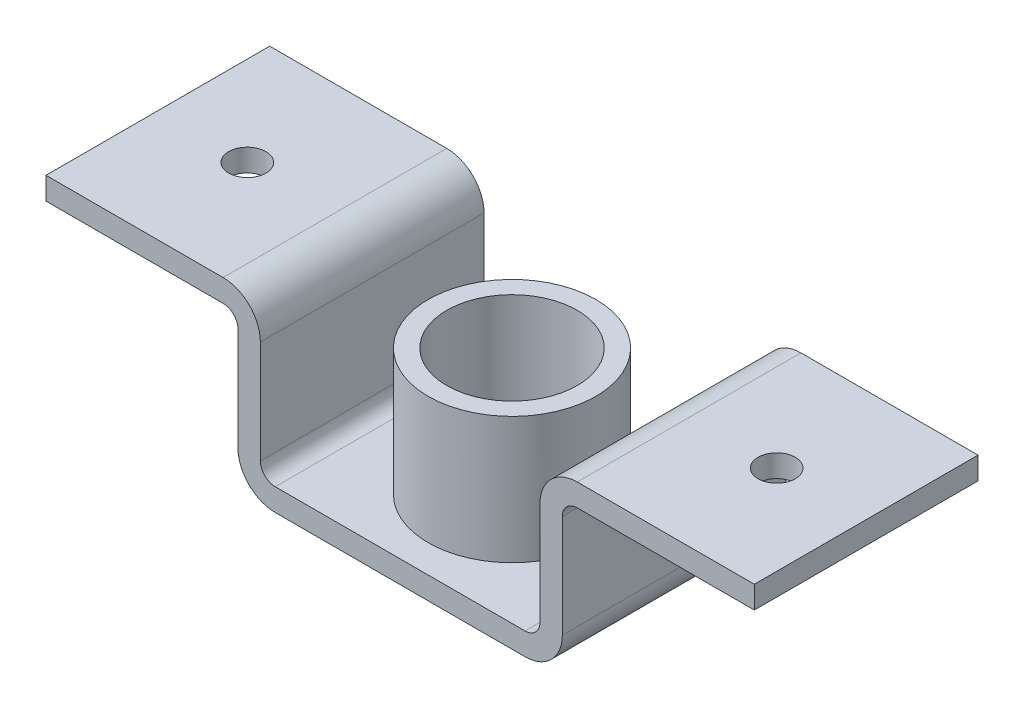
SolidWorks part; units mm, degrees
ref_plane "Front Plane" through (0, 0, 0) normal (0, 0, 1) x (1, 0, 0)
ref_plane "Top Plane" through (0, 0, 0) normal (0, 1, 0) x (1, 0, 0)
ref_plane "Right Plane" through (0, 0, 0) normal (1, 0, 0) x (0, 0, -1)
sketch "Sketch1" plane through (0, 0, 0) normal (0, 0, 1) x (1, 0, 0)
  line L0 (0, 437.3723) -> (0, -104.5891) construction
  line L1 (167.5, 0) -> (-167.5, 0)
  line L2 (-217.5, 50) -> (-217.5, 188)
  line L3 (-237.5, 208) -> (-475, 208)
  line L4 (-475, 208) -> (-475, 238)
  line L5 (-475, 238) -> (-237.5, 238)
  line L6 (-187.5, 188) -> (-187.5, 50)
  line L7 (-167.5, 30) -> (167.5, 30)
  line L8 (217.5, 50) -> (217.5, 188)
  line L9 (187.5, 188) -> (187.5, 50)
  line L10 (237.5, 208) -> (475, 208)
  line L11 (475, 238) -> (237.5, 238)
  line L12 (475, 208) -> (475, 238)
  arc A0 (-167.5, 0) -> (-217.5, 50) centre (-167.5, 50) cw
  arc A1 (-217.5, 188) -> (-237.5, 208) centre (-237.5, 188) ccw
  arc A2 (-237.5, 238) -> (-187.5, 188) centre (-237.5, 188) cw
  arc A3 (-187.5, 50) -> (-167.5, 30) centre (-167.5, 50) ccw
  arc A4 (167.5, 0) -> (217.5, 50) centre (167.5, 50) ccw
  arc A5 (187.5, 50) -> (167.5, 30) centre (167.5, 50) cw
  arc A6 (237.5, 238) -> (187.5, 188) centre (237.5, 188) ccw
  arc A7 (217.5, 188) -> (237.5, 208) centre (237.5, 188) cw
  point P21 (0, 30)
  point P22 (0, 0)
  dimension "D3" = 950
  dimension "D4" = 30
  dimension "D1" = 20
  dimension "D5" = 238
  dimension "D2" = 375
extrude "Boss-Extrude1" add sketch "Sketch1" along normal blind 300
sketch "Sketch3" plane through (0, 30, 0) normal (0, 1, 0) x (1, 0, 0)
  line L0 (0, 0) -> (0, -300) construction
  line L1 (167.5, -300) -> (-167.5, -300) construction
  line L2 (-167.5, -150) -> (167.5, -150) construction
  line L3 (-167.5, -300) -> (-167.5, 0) construction
  line L4 (167.5, -300) -> (167.5, 0) construction
  circle A0 centre (0, -150) radius 112.5
  circle A1 centre (0, -150) radius 87.5
  dimension "D1" = 225
  dimension "D2" = 175
extrude "Boss-Extrude2" add sketch "Sketch3" along normal blind 170
sketch "Sketch4" plane through (0, 30, 0) normal (0, 1, 0) x (1, 0, 0)
  circle A0 centre (0, -150) radius 37.5
  dimension "D1" = 75
extrude "Cut-Extrude1" cut sketch "Sketch4" against normal blind 170
sketch "Sketch5" plane through (0, 238, 0) normal (0, 1, 0) x (1, 0, 0)
  line L0 (475, -300) -> (475, 0) construction
  line L1 (475, -300) -> (237.5, -300) construction
  line L2 (-237.5, -300) -> (-475, -300) construction
  line L3 (-475, -300) -> (-475, 0) construction
  circle A0 centre (355, -150) radius 25
  circle A1 centre (-355, -150) radius 25
  dimension "D3" = 50
  dimension "D1" = 120
  dimension "D2" = 150
  dimension "D4" = 150
  dimension "D5" = 120
extrude "Cut-Extrude2" cut sketch "Sketch5" against normal blind 170
